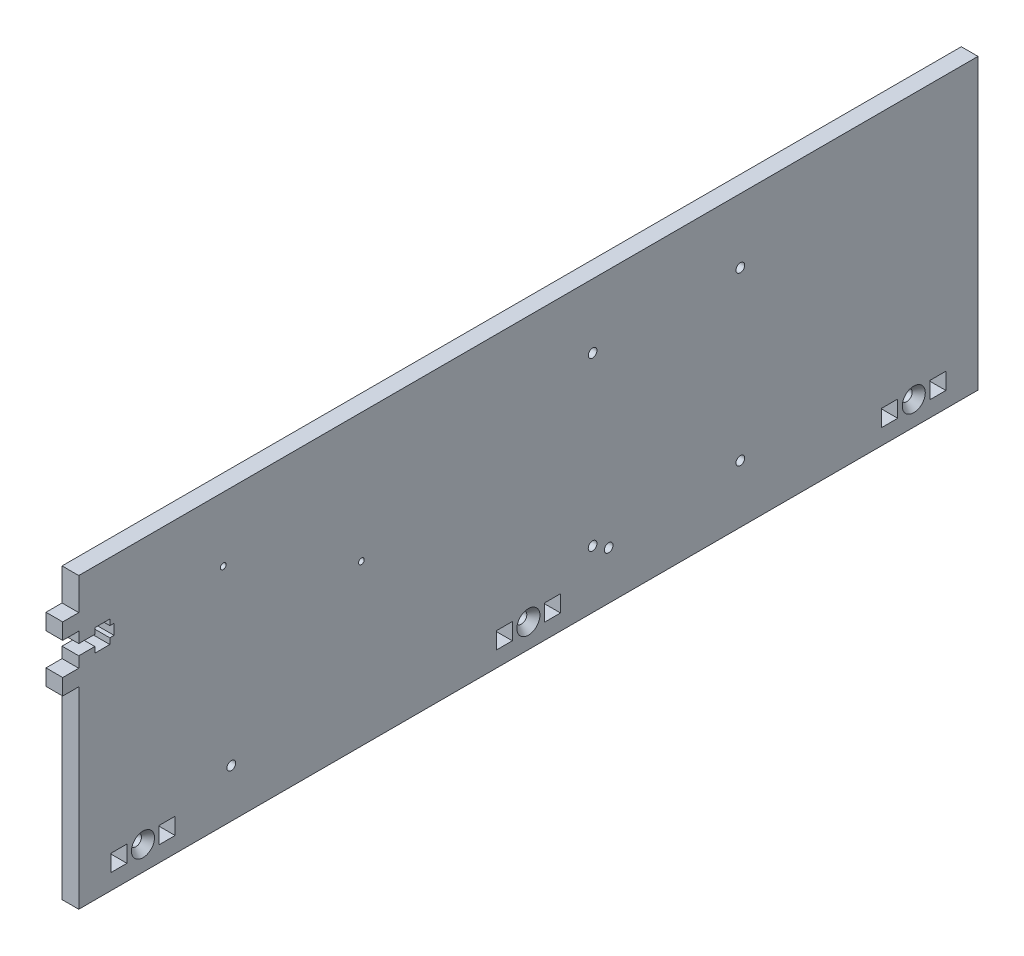
SolidWorks part; units mm, degrees
material "Acrylic (Blue)"
ref_plane "Front Plane" through (0, 0, 0) normal (0, 0, 1) x (1, 0, 0)
ref_plane "Top Plane" through (0, 0, 0) normal (0, 1, 0) x (1, 0, 0)
ref_plane "Right Plane" through (0, 0, 0) normal (1, 0, 0) x (0, 0, -1)
sketch "Sketch1" plane through (0, 0, 0) normal (1, 0, 0) x (0, 0, -1)
  line L0 (-139.7, 12.827) -> (-12.7, 12.827) construction
  line L1 (-177.8, 114.3) -> (177.8, 114.3)
  line L2 (-177.8, 114.3) -> (-177.8, 0)
  line L3 (-177.8, 0) -> (177.8, 0)
  line L4 (177.8, 114.3) -> (177.8, 0)
  line L5 (12.7, 12.827) -> (139.7, 12.827) construction
  line B0 (-146.05, 12.827) -> (-139.7, 12.827)
  line B1 (-139.7, 12.827) -> (-139.7, 6.223)
  line B2 (-139.7, 6.223) -> (-146.05, 6.223)
  line B3 (-146.05, 6.223) -> (-146.05, 12.827)
  line B4 (-165.1, 12.827) -> (-158.75, 12.827)
  line B5 (-158.75, 12.827) -> (-158.75, 6.223)
  line B6 (-158.75, 6.223) -> (-165.1, 6.223)
  line B7 (-165.1, 6.223) -> (-165.1, 12.827)
  circle B8 centre (-152.4, 9.525) radius 2.1526
  line B9 (6.35, 12.827) -> (12.7, 12.827)
  line B10 (12.7, 12.827) -> (12.7, 6.223)
  line B11 (12.7, 6.223) -> (6.35, 6.223)
  line B12 (6.35, 6.223) -> (6.35, 12.827)
  line B13 (-12.7, 12.827) -> (-6.35, 12.827)
  line B14 (-6.35, 12.827) -> (-6.35, 6.223)
  line B15 (-6.35, 6.223) -> (-12.7, 6.223)
  line B16 (-12.7, 6.223) -> (-12.7, 12.827)
  circle B17 centre (0, 9.525) radius 2.1526
  line B18 (158.75, 12.827) -> (165.1, 12.827)
  line B19 (165.1, 12.827) -> (165.1, 6.223)
  line B20 (165.1, 6.223) -> (158.75, 6.223)
  line B21 (158.75, 6.223) -> (158.75, 12.827)
  line B22 (139.7, 12.827) -> (146.05, 12.827)
  line B23 (146.05, 12.827) -> (146.05, 6.223)
  line B24 (146.05, 6.223) -> (139.7, 6.223)
  line B25 (139.7, 6.223) -> (139.7, 12.827)
  circle B26 centre (152.4, 9.525) radius 2.1526
  dimension "D1" = 114.3
  dimension "D2" = 355.6
  dimension "D3" = 12.7
  dimension "D4" = 12.7
  dimension "D5" = 9.525
sketch_block_instance "BOLT_HOLE-1"
sketch_block "BOLT_HOLE" parameters "D1"=4.3053, "D2"=6.35, "D3"=6.35, "D4"=6.604
sketch_block_instance "BOLT_HOLE-2"
sketch_block_instance "BOLT_HOLE-3"
extrude "Boss-Extrude1" add sketch "Sketch1" along normal blind 6.604
sketch "Sketch4" plane through (0, 0, 0) normal (-1, 0, 0) x (0, 0, 1)
  line L0 (177.8, 114.3) -> (177.8, 0) construction
  line L1 (-177.8, 114.3) -> (177.8, 114.3) construction
  line B0 (177.8, 90.9828) -> (171.45, 90.9828)
  line B1 (171.45, 90.9828) -> (171.45, 93.2688)
  line B2 (171.45, 93.2688) -> (165.5064, 93.2688)
  line B3 (165.5064, 93.2688) -> (165.5064, 90.9828)
  line B4 (165.5064, 90.9828) -> (163.83, 90.9828)
  line B5 (163.83, 90.9828) -> (163.83, 86.8172)
  line B6 (163.83, 86.8172) -> (165.5064, 86.8172)
  line B7 (165.5064, 86.8172) -> (165.5064, 84.5312)
  line B8 (165.5064, 84.5312) -> (171.45, 84.5312)
  line B9 (171.45, 84.5312) -> (171.45, 86.8172)
  line B10 (171.45, 86.8172) -> (177.8, 86.8172)
  line B11 (177.8, 86.8172) -> (177.8, 82.55)
  line B12 (177.8, 82.55) -> (184.15, 82.55)
  line B13 (184.15, 82.55) -> (184.15, 76.2)
  line B14 (184.15, 76.2) -> (177.8, 76.2)
  line B15 (177.8, 90.9828) -> (177.8, 95.25)
  line B16 (177.8, 95.25) -> (184.15, 95.25)
  line B17 (184.15, 95.25) -> (184.15, 101.6)
  line B18 (184.15, 101.6) -> (177.8, 101.6)
  line B19 (177.8, 86.8172) -> (177.8, 90.9828) construction
  dimension "D1" = 12.7
sketch_block_instance "NUT_HOLE-1"
sketch_block "NUT_HOLE" parameters "D1"=6.35, "D2"=4.1656, "D3"=25.4, "D4"=6.35, "D5"=8.7376, "D6"=5.9436, "D7"=6.35, "D8"=20.32
sketch "Sketch5" plane through (0, 0, 0) normal (-1, 0, 0) x (0, 0, 1)
  line L0 (177.8, 90.9828) -> (171.45, 90.9828) construction
  line L1 (171.45, 90.9828) -> (171.45, 93.2688) construction
  line L2 (171.45, 93.2688) -> (165.5064, 93.2688) construction
  line L3 (165.5064, 93.2688) -> (165.5064, 90.9828) construction
  line L4 (165.5064, 90.9828) -> (163.83, 90.9828) construction
  line L5 (163.83, 90.9828) -> (163.83, 86.8172) construction
  line L6 (163.83, 86.8172) -> (165.5064, 86.8172) construction
  line L7 (165.5064, 86.8172) -> (165.5064, 84.5312) construction
  line L8 (165.5064, 84.5312) -> (171.45, 84.5312) construction
  line L9 (171.45, 86.8172) -> (177.8, 86.8172) construction
  line L10 (171.45, 84.5312) -> (171.45, 86.8172) construction
  line L11 (177.8, 90.9828) -> (171.45, 90.9828)
  line L12 (171.45, 90.9828) -> (171.45, 93.2688)
  line L13 (171.45, 93.2688) -> (165.5064, 93.2688)
  line L14 (165.5064, 93.2688) -> (165.5064, 90.9828)
  line L15 (165.5064, 90.9828) -> (163.83, 90.9828)
  line L16 (163.83, 90.9828) -> (163.83, 86.8172)
  line L17 (163.83, 86.8172) -> (165.5064, 86.8172)
  line L18 (165.5064, 86.8172) -> (165.5064, 84.5312)
  line L19 (165.5064, 84.5312) -> (171.45, 84.5312)
  line L20 (171.45, 86.8172) -> (177.8, 86.8172)
  line L21 (171.45, 84.5312) -> (171.45, 86.8172)
  line L22 (177.8, 90.9828) -> (177.8, 86.8172)
extrude "Cut-Extrude1" cut sketch "Sketch5" against normal through all
sketch "Sketch6" plane through (0, 0, 0) normal (-1, 0, 0) x (0, 0, 1)
  line L0 (184.15, 101.6) -> (177.8, 101.6) construction
  line L1 (184.15, 95.25) -> (184.15, 101.6) construction
  line L2 (177.8, 95.25) -> (184.15, 95.25) construction
  line L3 (184.15, 76.2) -> (177.8, 76.2) construction
  line L4 (177.8, 82.55) -> (184.15, 82.55) construction
  line L5 (184.15, 82.55) -> (184.15, 76.2) construction
  line L6 (184.15, 101.6) -> (177.8, 101.6)
  line L7 (184.15, 95.25) -> (184.15, 101.6)
  line L8 (177.8, 95.25) -> (184.15, 95.25)
  line L9 (184.15, 76.2) -> (177.8, 76.2)
  line L10 (177.8, 82.55) -> (184.15, 82.55)
  line L11 (184.15, 82.55) -> (184.15, 76.2)
  line L12 (177.8, 101.6) -> (177.8, 95.25)
  line L13 (177.8, 82.55) -> (177.8, 76.2)
extrude "Boss-Extrude2" add sketch "Sketch6" against normal up to surface (6.604 mm away) up to face at (6.604, 80.9625, 126.9428)
hole_wizard "CSK for #8 Flat Head Socket Cap Screw2" positions "Sketch8" profile "Sketch7" countersink size "#8" standard "ANSI Inch" end condition through all
sketch "Sketch8" plane through (6.604, 0, 0) normal (1, 0, 0) x (0, 0, -1)
  circle A2 centre (0, 9.525) radius 2.1526 construction
  point P0 (-152.4, 9.525)
  point P3 (0, 9.525)
  point P5 (152.4, 9.525)
sketch "Sketch7" plane through (6.604, 9.525, 152.4) normal (0, 1, 0) x (0, 0, -1)
  line L0 (0, 0) -> (0, 6.604)
  line L1 (0, 6.604) -> (2.1526, 6.604)
  line L2 (2.1526, 6.604) -> (2.1526, 2.7685)
  line L3 (2.1526, 2.7685) -> (4.5593, 0)
  line L5 (4.5593, 0) -> (0, 0)
  line L6 (-2.1526, 2.7685) -> (-4.5593, 0) construction
  line L11 (0, -6.35) -> (0, 107.95) construction
  dimension "Thru Hole Dia." = 4.3053
  dimension "Thru Hole Depth" = 6.604
  dimension "Near C'Sink Dia." = 9.1186
  dimension "Near C'Sink Angle" = 82
hole_wizard "#4-40 Tapped Hole2" positions "Sketch10" profile "Sketch11" tap size "#4-40" standard "ANSI Inch"
sketch "Sketch10" plane through (0, 0, 0) normal (-1, 0, 0) x (0, 0, 1)
  line L0 (-177.8, 114.3) -> (177.8, 114.3) construction
  line L1 (177.8, 114.3) -> (177.8, 101.6) construction
  point P0 (120.65, 88.9)
  point P2 (66.04, 63.2968)
  dimension "D1" = 25.4
  dimension "D2" = 25.6032
  dimension "D3" = 57.15
  dimension "D4" = 54.61
sketch "Sketch11" plane through (0, 88.9, 120.65) normal (0, 1, 0) x (0, 0, 1)
  line L0 (0, 0) -> (0, 8.2738)
  line L1 (0, 8.2738) -> (1.1303, 7.5946)
  line L2 (1.1303, 7.5946) -> (1.1303, 0)
  line L5 (1.1303, 0) -> (0, 0)
  line L10 (0, 8.2738) -> (-1.1303, 7.5946) construction
  line L11 (0, -6.35) -> (0, 107.95) construction
  dimension "Tap Drill Dia." = 2.2606
  dimension "Tap Drill Depth" = 7.5946
  dimension "Drill Angle" = 118
hole_wizard "#8-32 Tapped Hole1" positions "Sketch13" profile "Sketch12" tap size "#8-32" standard "ANSI Inch"
sketch "Sketch13" plane through (0, 0, 0) normal (-1, 0, 0) x (0, 0, 1)
  line L1 (-83.82, 88.9) -> (-25.4, 88.9) construction
  line L2 (-83.82, 88.9) -> (-83.82, 22.86) construction
  line L3 (-83.82, 22.86) -> (-25.4, 22.86) construction
  line L4 (-25.4, 88.9) -> (-25.4, 22.86) construction
  line L5 (177.8, 76.2) -> (177.8, 0) construction
  line L6 (-177.8, 114.3) -> (177.8, 114.3) construction
  point P0 (-83.82, 88.9)
  point P2 (-25.4, 88.9)
  point P4 (-83.82, 22.86)
  point P6 (-25.4, 22.86)
  dimension "D1" = 58.42
  dimension "D2" = 66.04
  dimension "D3" = 203.2
  dimension "D4" = 25.4
sketch "Sketch12" plane through (0, 88.9, -83.82) normal (0, 1, 0) x (0, 0, 1)
  line L0 (0, 0) -> (0, 11.7566)
  line L1 (0, 11.7566) -> (1.7272, 10.7188)
  line L2 (1.7272, 10.7188) -> (1.7272, 0)
  line L5 (1.7272, 0) -> (0, 0)
  line L10 (0, 11.7566) -> (-1.7272, 10.7188) construction
  line L11 (0, -6.35) -> (0, 107.95) construction
  dimension "Tap Drill Dia." = 3.4544
  dimension "Tap Drill Depth" = 10.7188
  dimension "Drill Angle" = 118
hole_wizard "#8-32 Tapped Hole2" positions "Sketch15" profile "Sketch14" tap size "#8-32" standard "ANSI Inch"
sketch "Sketch15" plane through (6.604, 0, 0) normal (1, 0, 0) x (0, 0, -1)
  line L0 (-177.8, 19.05) -> (-117.475, 19.05) construction
  line L1 (-177.8, 76.2) -> (-177.8, 0) construction
  line L2 (-117.475, 19.05) -> (31.75, 19.05) construction
  line L4 (-177.8, -3.175) -> (-9.4723, -3.175) construction
  line L6 (-177.8, 0) -> (177.8, 0) construction
  point P2 (-117.475, 19.05)
  point P6 (31.75, 19.05)
  dimension "D1" = 3.175
  dimension "D2" = 60.325
  dimension "D3" = 209.55
  dimension "D4" = 22.225
sketch "Sketch14" plane through (6.604, 19.05, 117.475) normal (0, 1, 0) x (0, 0, -1)
  line L0 (0, 0) -> (0, 11.7566)
  line L1 (0, 11.7566) -> (1.7272, 10.7188)
  line L2 (1.7272, 10.7188) -> (1.7272, 0)
  line L5 (1.7272, 0) -> (0, 0)
  line L10 (0, 11.7566) -> (-1.7272, 10.7188) construction
  line L11 (0, -6.35) -> (0, 107.95) construction
  dimension "Tap Drill Dia." = 3.4544
  dimension "Tap Drill Depth" = 10.7188
  dimension "Drill Angle" = 118
other "Move Face1" [suppressed] parameters "D1"=0.0508
